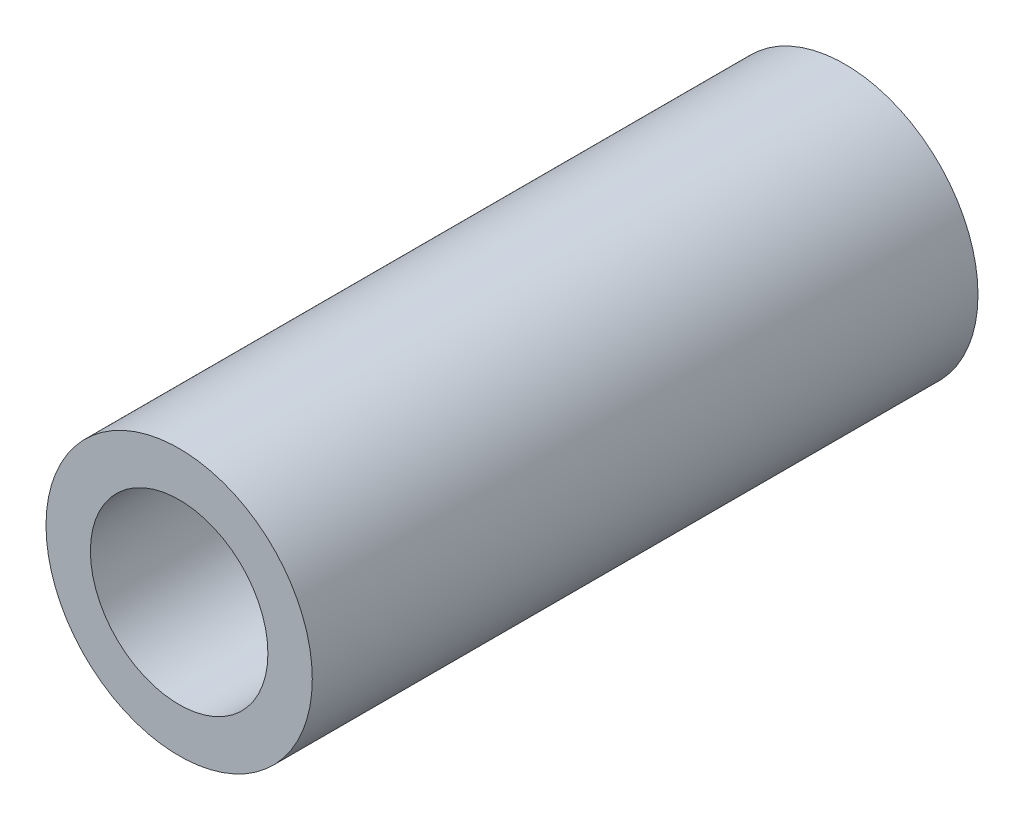
SolidWorks part; units mm, degrees
material "PVC Rigid"
ref_plane "Front Plane" through (0, 0, 0) normal (0, 0, 1) x (1, 0, 0)
ref_plane "Top Plane" through (0, 0, 0) normal (0, 1, 0) x (1, 0, 0)
ref_plane "Right Plane" through (0, 0, 0) normal (1, 0, 0) x (0, 0, -1)
sketch "Sketch1" plane through (0, 0, 0) normal (0, 0, 1) x (1, 0, 0)
  circle A0 centre (0, 0) radius 7.62
  circle A2 centre (0, 0) radius 5.08
  dimension "D1" = 15.24
  dimension "D2" = 10.16
extrude "Boss-Extrude1" add sketch "Sketch1" along normal blind 38.1
